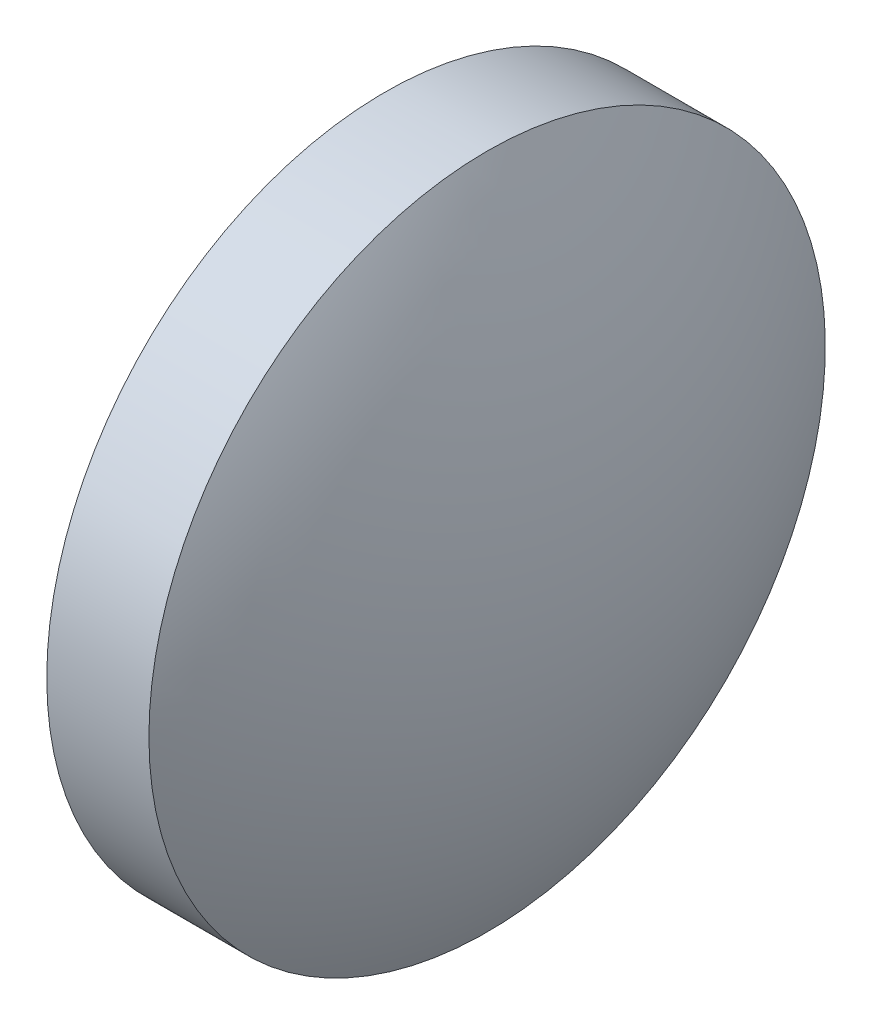
SolidWorks part; units mm, degrees
ref_plane "前视基准面" through (0, 0, 0) normal (0, 0, 1) x (1, 0, 0)
ref_plane "上视基准面" through (0, 0, 0) normal (0, 1, 0) x (1, 0, 0)
ref_plane "右视基准面" through (0, 0, 0) normal (1, 0, 0) x (0, 0, -1)
sketch "草图1" plane through (0, 0, 0) normal (0, 0, 1) x (1, 0, 0)
  line L0 (579.2776, 182.9834) -> (584.6559, 182.9834) construction
  line L1 (580.5091, 182.9834) -> (580.5091, 187.9834)
  line L2 (580.5091, 187.9834) -> (582.0191, 187.9834)
  line L3 (580.5091, 182.9834) -> (583.3091, 182.9834)
  arc A0 (583.3091, 182.9834) -> (582.0191, 187.9834) centre (572.9742, 182.9834) ccw
revolve "旋转1" add sketch "草图1" angle 360 about L0
